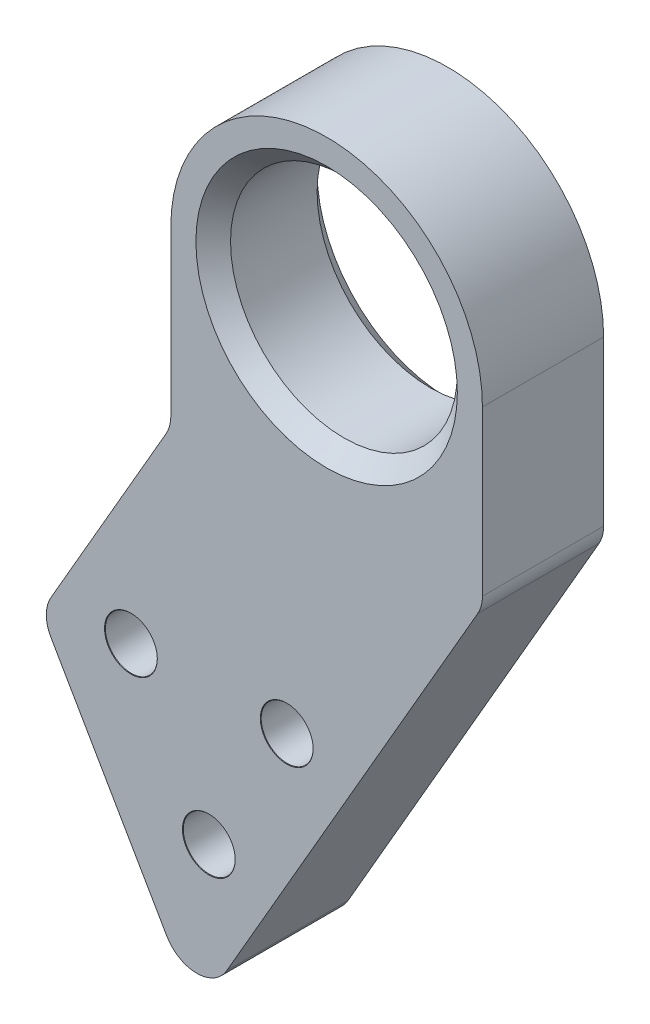
SolidWorks part; units mm, degrees
material "ABS"
ref_plane "Front Plane" through (0, 0, 0) normal (0, 0, 1) x (1, 0, 0)
ref_plane "Top Plane" through (0, 0, 0) normal (0, 1, 0) x (1, 0, 0)
ref_plane "Right Plane" through (0, 0, 0) normal (1, 0, 0) x (0, 0, -1)
sketch "Sketch1" plane through (0, 0, 0) normal (0, 0, 1) x (1, 0, 0)
  line L0 (-9, 0) -> (-9, -10)
  line L2 (9, -10) -> (9, 0)
  line L6 (-9, -10) -> (-16.5, -22.9904)
  line L7 (-16.5, -22.9904) -> (-7.5, -38.5788)
  line L8 (-7.5, -38.5788) -> (9, -10)
  circle A0 centre (0, 0) radius 6.55
  arc A1 (-9, 0) -> (9, 0) centre (0, 0) cw
  point P6 (0, 0)
  point P10 (-5.8076, -45.6475)
  point P11 (-5.6199, -45.3224)
  dimension "D1" = 13.1
  dimension "D2" = 9
  dimension "D3" = 10
  dimension "D4" = 18
  dimension "D5" = 150
  dimension "D6" = 15
extrude "Boss-Extrude1" add sketch "Sketch1" along normal blind 7
chamfer "Chamfer1" distance 1 angle 45 2 edges at (6.55, 0, 7) (6.55, 0, 0)
fillet "Fillet1" radius 2 4 edges at (9, -10, 3.5) (-7.5, -38.5788, 3.5) (-16.5, -22.9904, 3.5) (-9, -10, 3.5)
hole_wizard "Ø3.0mm Dowel Hole1" positions "Sketch2" profile "Sketch3" hole size "Ø3.0" standard "ANSI Metric" end condition through all
sketch "Sketch2" plane through (0, 0, 7) normal (0, 0, 1) x (1, 0, 0)
  line L0 (-15.9226, -23.9904) -> (-9.2321, -35.5788) construction
  line L1 (-9.2679, -10.4641) -> (-15.9226, -21.9904) construction
  point P0 (-11.3038, -21.9904)
  point P2 (-6.8038, -29.7846)
  point P9 (-2.3038, -21.9904)
  point P12 (0, 0)
  point P13 (-1.3367, -22.5966)
  point P14 (0, 0)
  point P15 (-2.5689, -22.2232)
  dimension "D1" = 9
  dimension "D2" = 5
  dimension "D3" = 5
  dimension "D4" = 4
  dimension "D5" = 9
  dimension "D6" = 9
sketch "Sketch3" plane through (-11.3038, -21.9904, 7) normal (1, 0, 0) x (0, -1, 0)
  line L0 (0, 0) -> (0, 7)
  line L1 (0, 7) -> (1.5, 7)
  line L2 (1.5, 7) -> (1.5, 0.025)
  line L3 (1.5, 0.025) -> (1.525, 0)
  line L5 (1.525, 0) -> (0, 0)
  line L6 (-1.5, 0.025) -> (-1.525, 0) construction
  line L11 (0, -6.35) -> (0, 107.95) construction
  dimension "Thru Hole Dia." = 3
  dimension "Thru Hole Depth" = 7
  dimension "Near C'Sink Dia." = 3.05
  dimension "Near C'Sink Angle" = 90
